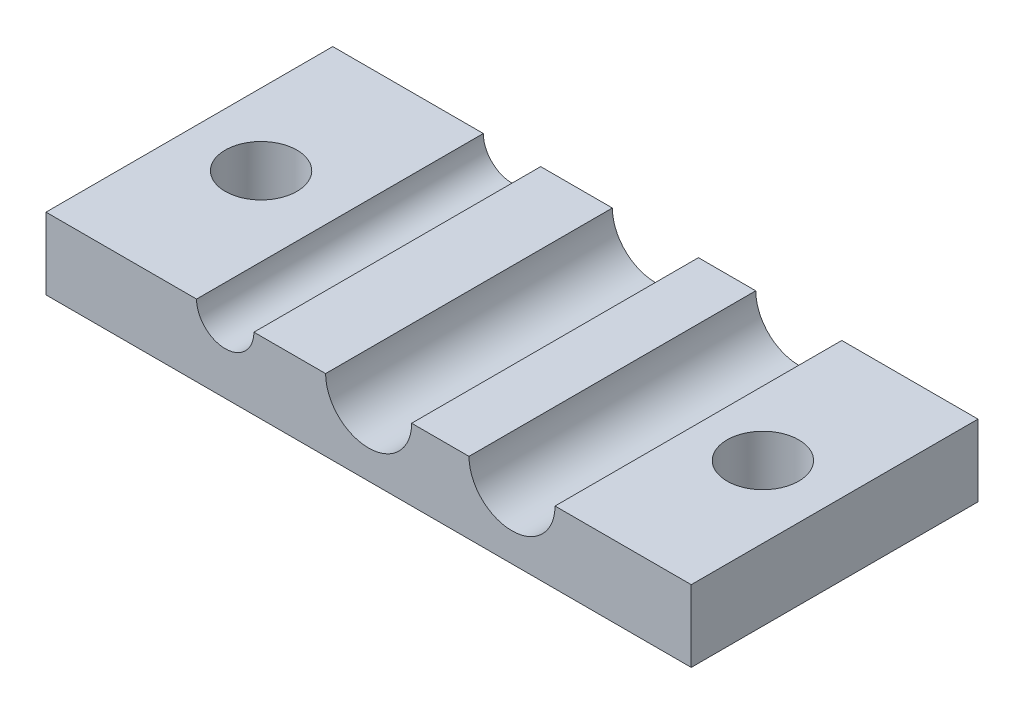
SolidWorks part; units mm, degrees
ref_plane "Front Plane" through (0, 0, 0) normal (0, 0, 1) x (1, 0, 0)
ref_plane "Top Plane" through (0, 0, 0) normal (0, 1, 0) x (1, 0, 0)
ref_plane "Right Plane" through (0, 0, 0) normal (1, 0, 0) x (0, 0, -1)
sketch "Sketch1" plane through (0, 0, 0) normal (0, 0, 1) x (1, 0, 0)
  line L0 (0, 0) -> (0, 22.5) construction
  line L1 (-22.5, -22.5) -> (22.5, -22.5)
  line L2 (-22.5, -22.5) -> (-22.5, 22.5)
  line L3 (-22.5, 22.5) -> (22.5, 22.5) construction
  line L4 (22.5, -22.5) -> (22.5, 22.5)
  line L5 (-22.5, -22.5) -> (22.5, 22.5) construction
  line L6 (-22.5, 22.5) -> (22.5, -22.5) construction
  line L7 (-22.5, 22.5) -> (-12, 22.5)
  line L8 (-8, 22.5) -> (-3, 22.5)
  line L9 (3, 22.5) -> (7, 22.5)
  line L10 (13, 22.5) -> (22.5, 22.5)
  circle A0 centre (-10, 22.5) radius 2 construction
  circle A1 centre (0, 22.5) radius 3 construction
  circle A2 centre (10, 22.5) radius 3 construction
  arc A3 (-12, 22.5) -> (-8, 22.5) centre (-10, 22.5) ccw
  arc A4 (-3, 22.5) -> (3, 22.5) centre (0, 22.5) ccw
  arc A5 (7, 22.5) -> (13, 22.5) centre (10, 22.5) ccw
  point P0 (0, 0)
  dimension "D3" = 4
  dimension "D4" = 6
  dimension "D5" = 6
  dimension "D1" = 45
  dimension "D2" = 45
  dimension "D6" = 10
  dimension "D7" = 10
extrude "Boss-Extrude1" add sketch "Sketch1" along normal blind 20
sketch "Sketch2" plane through (0, 22.5, 0) normal (0, 1, 0) x (1, 0, 0)
  line L0 (-22.5, -10) -> (22.5, -10) construction
  line L1 (-22.5, -20) -> (-22.5, 0) construction
  line L2 (22.5, -20) -> (22.5, 0) construction
  line L3 (0, 0) -> (0, -20) construction
  line L4 (-3, -20) -> (3, -20) construction
  circle A0 centre (-17.5, -10) radius 2.5
  circle A1 centre (17.5, -10) radius 2.5
  dimension "D1" = 5
  dimension "D2" = 5
extrude "Cut-Extrude1" cut sketch "Sketch2" against normal blind 20
sketch "Sketch3" plane through (0, 0, 0) normal (0, 0, -1) x (-1, 0, 0)
  line L0 (22.5, 22.5) -> (22.5, -22.5) construction
  line L1 (-22.5, -22.5) -> (22.5, -22.5)
  line L2 (-22.5, -22.5) -> (-22.5, 17.5)
  line L3 (-22.5, 17.5) -> (22.5, 17.5)
  line L4 (22.5, -22.5) -> (22.5, 17.5)
  line L5 (-22.5, 22.5) -> (-13, 22.5) construction
  dimension "D1" = 5
extrude "Cut-Extrude2" cut sketch "Sketch3" against normal blind 20
